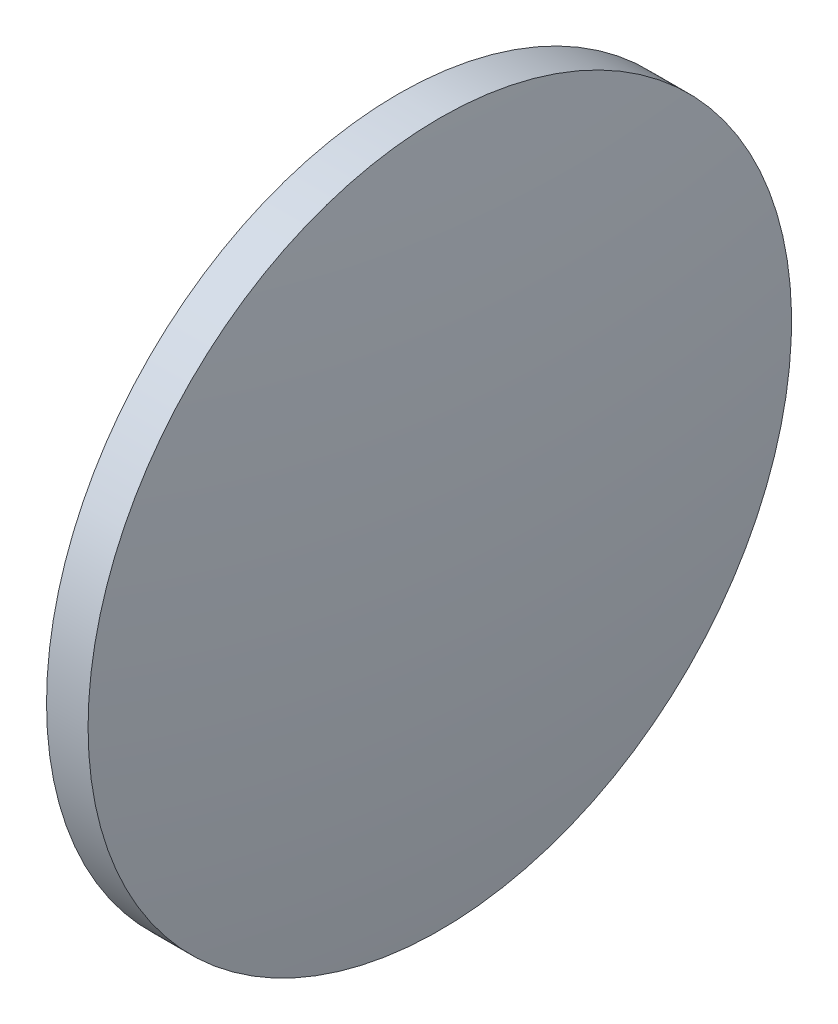
SolidWorks part; units mm, degrees
ref_plane "前视基准面" through (0, 0, 0) normal (0, 0, 1) x (1, 0, 0)
ref_plane "上视基准面" through (0, 0, 0) normal (0, 1, 0) x (1, 0, 0)
ref_plane "右视基准面" through (0, 0, 0) normal (1, 0, 0) x (0, 0, -1)
sketch "草图1" plane through (0, 0, 0) normal (0, 0, 1) x (1, 0, 0)
  line L0 (165.7441, 97.2322) -> (179.7312, 97.2322) construction
  line L1 (171.4164, 122.6322) -> (174.4164, 122.6322)
  line L2 (174.4164, 122.6322) -> (174.4164, 71.8322)
  line L3 (174.4164, 71.8322) -> (171.4164, 71.8322)
  line L4 (171.4164, 71.8322) -> (171.4164, 122.6322)
  arc A0 (171.4164, 122.6322) -> (171.4164, 71.8322) centre (354.8742, 97.2322) ccw
  arc A1 (174.4164, 71.8322) -> (174.4164, 122.6322) centre (-9.0414, 97.2322) ccw
  dimension "D1" = 50.8
  dimension "D2" = 3
revolve "旋转1" add sketch "草图1" angle 360 about L0
